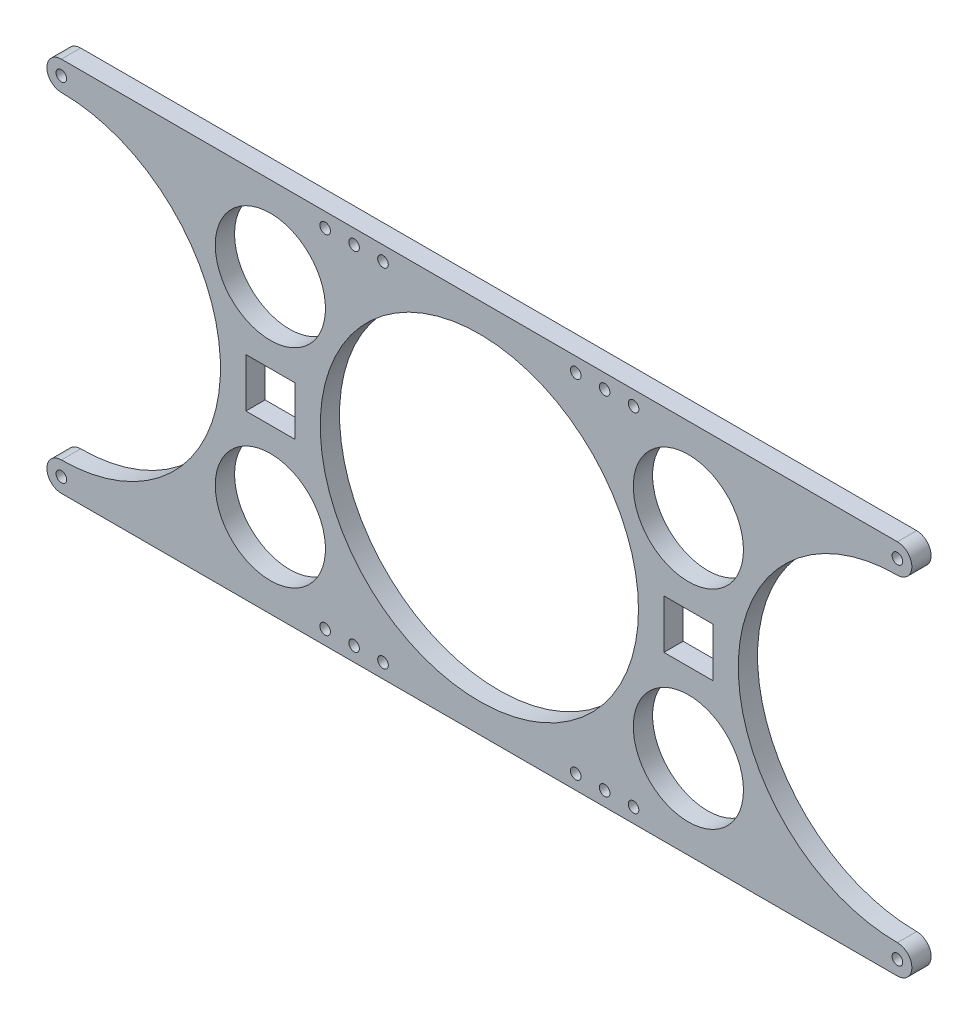
SolidWorks part; units mm, degrees
material "1060 Alloy"
ref_plane "Front Plane" through (0, 0, 0) normal (0, 0, 1) x (1, 0, 0)
ref_plane "Top Plane" through (0, 0, 0) normal (0, 1, 0) x (1, 0, 0)
ref_plane "Right Plane" through (0, 0, 0) normal (1, 0, 0) x (0, 0, -1)
sketch "Sketch1" plane through (0, 0, 0) normal (0, 0, 1) x (1, 0, 0)
  line L0 (0, 0) -> (216.8683, 0) construction
  line L1 (108.4342, -53.975) -> (108.4342, 53.975) construction
  line L2 (0, 82.55) -> (216.8683, 82.55) construction
  line L3 (216.8683, 82.55) -> (216.8683, -82.55) construction
  line L4 (-216.8683, 97.55) -> (216.8683, 97.55)
  line L5 (-216.8683, -97.55) -> (216.8683, -97.55)
  line L6 (0, 82.55) -> (0, 0) construction
  line L7 (-95.7342, -12.7) -> (-95.7342, 12.7)
  line L8 (95.7342, -12.7) -> (121.1342, -12.7)
  line L9 (95.7342, -12.7) -> (95.7342, 12.7)
  line L10 (95.7342, 12.7) -> (121.1342, 12.7)
  line L11 (121.1342, -12.7) -> (121.1342, 12.7)
  line L12 (95.7342, -12.7) -> (121.1342, 12.7) construction
  line L13 (95.7342, 12.7) -> (121.1342, -12.7) construction
  line L14 (-95.7342, 12.7) -> (-121.1342, 12.7)
  line L15 (-121.1342, -12.7) -> (-121.1342, 12.7)
  line L16 (-95.7342, -12.7) -> (-121.1342, -12.7)
  line L17 (0, 82.55) -> (0, 97.55) construction
  line L18 (50, 90.05) -> (80, 90.05) construction
  line L19 (80, 90.05) -> (90.7455, 76.417) construction
  circle A0 centre (0, 0) radius 82.55
  arc A1 (216.8683, 82.55) -> (216.8683, -82.55) centre (216.8683, 0) ccw
  circle A2 centre (108.4342, 53.975) radius 28.575
  circle A3 centre (108.4342, -53.975) radius 28.575
  arc A4 (216.8683, 82.55) -> (216.8683, 97.55) centre (216.8683, 90.05) ccw
  arc A5 (216.8683, -82.55) -> (216.8683, -97.55) centre (216.8683, -90.05) cw
  circle A6 centre (-108.4342, -53.975) radius 28.575
  arc A7 (-216.8683, -82.55) -> (-216.8683, -97.55) centre (-216.8683, -90.05) ccw
  arc A8 (-216.8683, 82.55) -> (-216.8683, 97.55) centre (-216.8683, 90.05) cw
  circle A9 centre (-108.4342, 53.975) radius 28.575
  arc A10 (-216.8683, 82.55) -> (-216.8683, -82.55) centre (-216.8683, 0) cw
  point P9 (108.4342, 0)
  point P10 (108.4342, 0)
  point P24 (0, -97.55)
  point P25 (0, 97.55)
  point P30 (108.4342, 0)
  point P31 (216.8683, 90.05)
  point P32 (216.8683, -90.05)
  point P33 (-216.8683, -90.05)
  point P34 (-216.8683, 90.05)
  point P46 (65, 90.05)
  point P48 (-80, 90.05)
  point P49 (-65, 90.05)
  point P50 (50, 90.05)
  point P51 (80, 90.05)
  point P52 (-50, 90.05)
  point P54 (80, -90.05)
  point P55 (65, -90.05)
  point P56 (50, -90.05)
  point P57 (-50, -90.05)
  point P58 (-65, -90.05)
  point P59 (-80, -90.05)
  dimension "D1" = 165.1
  dimension "D3" = 57.15
  dimension "D2" = 10
  dimension "D4" = 15
  dimension "D5" = 25.4
  dimension "D7" = 50
  dimension "D6" = 15
extrude "Boss-Extrude1" add sketch "Sketch1" along normal mid plane 10
sketch "Sketch2" plane through (0, 0, 0) normal (0, 1, 0) x (1, 0, 0)
  line L0 (0, 5) -> (0, -5) construction
  line L2 (216.8683, 5) -> (-216.8683, 5) construction
  line L3 (216.8683, -5) -> (-216.8683, -5) construction
  line L4 (0, 0) -> (110.0348, 0) construction
  line L5 (110.0348, 5) -> (110.0348, -5) construction
hole_wizard "M5 Clearance Hole1" positions "Sketch3" profile "Sketch4" hole size "M5" standard "ANSI Metric" end condition through all
sketch "Sketch3" plane through (0, 0, 5) normal (0, 0, 1) x (1, 0, 0)
  point P0 (-80, 90.05)
  point P3 (-65, 90.05)
  point P6 (-50, 90.05)
  point P9 (50, 90.05)
  point P12 (65, 90.05)
  point P15 (80, 90.05)
  point P18 (-80, -90.05)
  point P21 (-65, -90.05)
  point P24 (-50, -90.05)
  point P27 (50, -90.05)
  point P30 (65, -90.05)
  point P33 (80, -90.05)
  point P37 (-216.8683, 90.05)
  point P40 (216.8683, 90.05)
  point P43 (-216.8683, -90.05)
  point P46 (216.8683, -90.05)
sketch "Sketch4" plane through (-80, 90.05, 5) normal (1, 0, 0) x (0, -1, 0)
  line L0 (0, 0) -> (0, 10)
  line L1 (0, 10) -> (2.75, 10)
  line L2 (2.75, 10) -> (2.75, 0)
  line L5 (2.75, 0) -> (0, 0)
  line L11 (0, -6.35) -> (0, 107.95) construction
  dimension "Thru Hole Dia." = 5.5
  dimension "Thru Hole Depth" = 10
equation "\"D1@Sketch1\"=152.40 + (6.35*2)"
